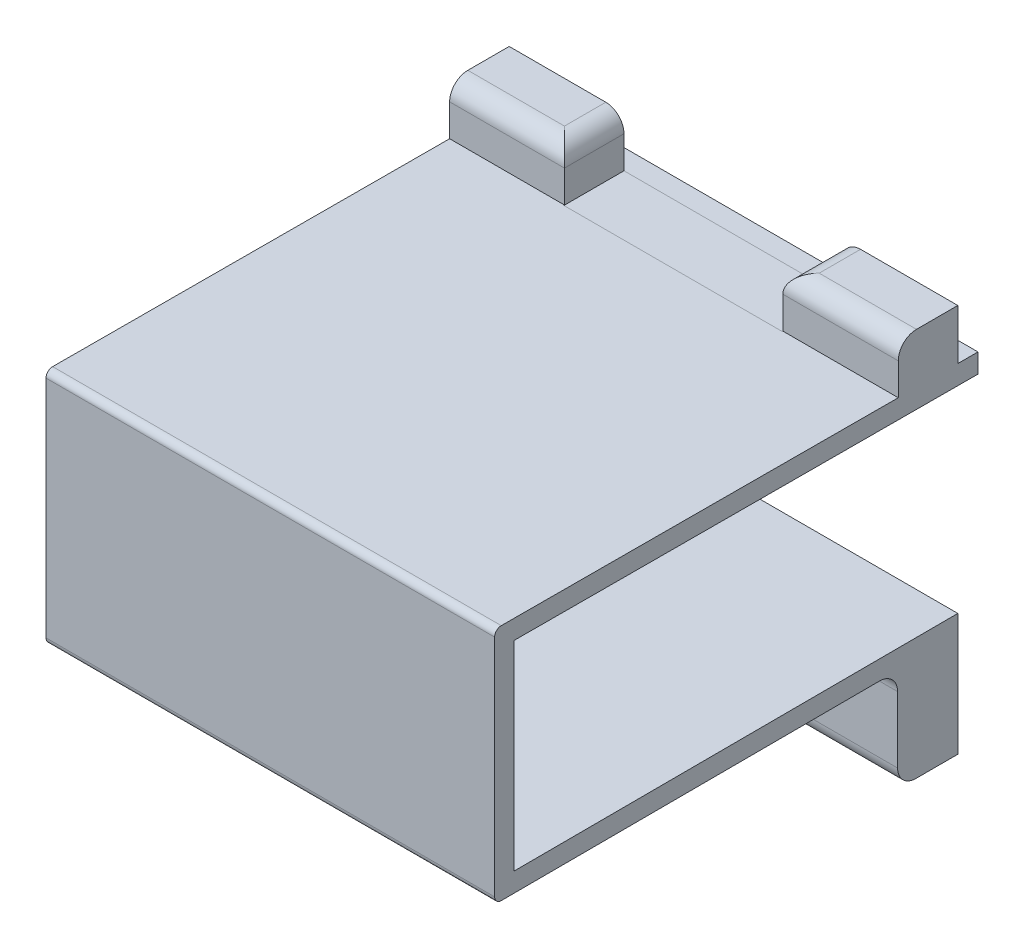
SolidWorks part; units mm, degrees
ref_plane "Ebene vorne" through (0, 0, 0) normal (0, 0, 1) x (1, 0, 0)
ref_plane "Ebene oben" through (0, 0, 0) normal (0, 1, 0) x (1, 0, 0)
ref_plane "Ebene rechts" through (0, 0, 0) normal (1, 0, 0) x (0, 0, -1)
sketch "Skizze1" plane through (0, 0, 0) normal (1, 0, 0) x (0, 0, -1)
  line L0 (0, 0) -> (0, 50000) construction
  line L1 (-67.1, 29.9917) -> (3.05, 29.7913)
  line L2 (-70, -3.1) -> (-70, 32.9)
  line L3 (0, 32.7046) -> (0, 40.3046)
  line L4 (3.05, 29.7913) -> (3.05, 32.6958)
  line L5 (3.05, 32.6958) -> (0, 32.7046)
  line L6 (-67.1, 29.9917) -> (-67.1, -0.1917)
  line L7 (-67.1, -0.1917) -> (0, 0)
  line L8 (0, 0) -> (0, -18.44)
  line L9 (0, 40.3046) -> (-9, 40.3046)
  line L10 (-9, 40.3046) -> (-9, 32.7257)
  line L11 (-9, 32.7257) -> (-70, 32.9)
  line L12 (0, -18.44) -> (-9.1, -18.44)
  line L13 (-9.1, -18.44) -> (-9.1, -2.926)
  line L14 (-9.1, -2.926) -> (-70, -3.1)
  line L15 (0, 29.8) -> (0, 0) construction
  line L16 (0, 14.9) -> (-70, 14.9) construction
  point P20 (-70, 14.9)
  dimension "D1" = 18.44
  dimension "D2" = 9.1
  dimension "D3" = 2.9
  dimension "D4" = 2.9
  dimension "D5" = 2.9046
  dimension "D6" = 29.8
  dimension "D7" = 3.05
  dimension "D8" = 36
  dimension "D9" = 7.6
  dimension "D10" = 70
  dimension "D11" = 9
  dimension "D12" = 2.9
extrude "Aufsatz-Linear austragen1" add sketch "Skizze1" against normal blind 67.8
sketch "Skizze3" plane through (0, 0, 0) normal (0, 0, 1) x (1, 0, 0)
  line L0 (-67.8, 40.3046) -> (0, 40.3046) construction
  line L1 (-17.45, 40.3046) -> (-50.45, 40.3046)
  line L2 (-17.45, 40.3046) -> (-17.45, 32.7046)
  line L3 (-17.45, 32.7046) -> (-50.45, 32.7046)
  line L4 (-50.45, 40.3046) -> (-50.45, 32.7046)
  line L5 (-67.8, 32.7046) -> (0, 32.7046) construction
  line L6 (-67.8, -18.44) -> (0, -18.44) construction
  line L7 (-17.45, -18.44) -> (-50.45, -18.44)
  line L8 (-17.45, -18.44) -> (-17.45, -2.09)
  line L9 (-17.45, -2.09) -> (-50.45, -2.09)
  line L10 (-50.45, -18.44) -> (-50.45, -2.09)
  dimension "D1" = 33
  dimension "D2" = 33
  dimension "D3" = 17.45
  dimension "D4" = 17.45
  dimension "D5" = 2.09
extrude "Schnitt-Linear austragen1" cut sketch "Skizze3" along normal up to surface (9.1 mm away) up to face at (-33.9, -10.683, 9.1)
ref_plane "Ebene1" through (0, 0, 1) normal (0, 0, 1) x (1, 0, 0)
sketch "Skizze4" plane through (0, 0, 1) normal (0, 0, 1) x (1, 0, 0)
  line L1 (-32.25, 0) -> (-35, 0)
  line L2 (-32.25, 0) -> (-32.25, 30.2)
  line L3 (-32.25, 30.2) -> (-35, 30.2)
  line L4 (-35, 0) -> (-35, 30.2)
  line L6 (26.1789, 0) -> (-98.5227, 0) construction
  dimension "D1" = 32.25
  dimension "D2" = 2.75
  dimension "D3" = 30.2
extrude "Aufsatz-Linear austragen2" add sketch "Skizze4" along normal up to surface (66.1 mm away) up to face at (-33.9, 14.9, 67.1)
fillet "Verrundung1" radius 2.75 10 edges at (-59.125, 40.3046, 9) (-50.45, 40.3046, 4.5) (-8.725, 40.3046, 9) (-17.45, 40.3046, 4.5) (-8.725, -2.926, 9.1) (-8.725, -18.44, 9.1) (-17.45, -18.44, 4.55) (-50.45, -18.44, 4.55) (-59.125, -18.44, 9.1) (-59.125, -2.926, 9.1)
fillet "Verrundung3" radius 1 2 edges at (-33.9, 32.9, 70) (-33.9, -3.1, 70)
sketch "Skizze6" plane through (0, 0, 0) normal (1, 0, 0) x (0, 0, -1)
  line L0 (-67.1, 29.9917) -> (-34, 29.8971)
  line L1 (-67.1, 29.9917) -> (-1, 29.8029) construction
  line L2 (-34, 29.8971) -> (-34, -0.0971)
  line L3 (0, 0) -> (-67.1, -0.1917) construction
  line L4 (-34, -0.0971) -> (-67.1, -0.1917)
  line L5 (-67.1, -0.1917) -> (-67.1, 29.9917)
  dimension "D1" = 34
extrude "Schnitt-Linear austragen2" cut sketch "Skizze6" against normal up to surface (35 mm away) up to face at (-35, 14.9486, 34.05)
